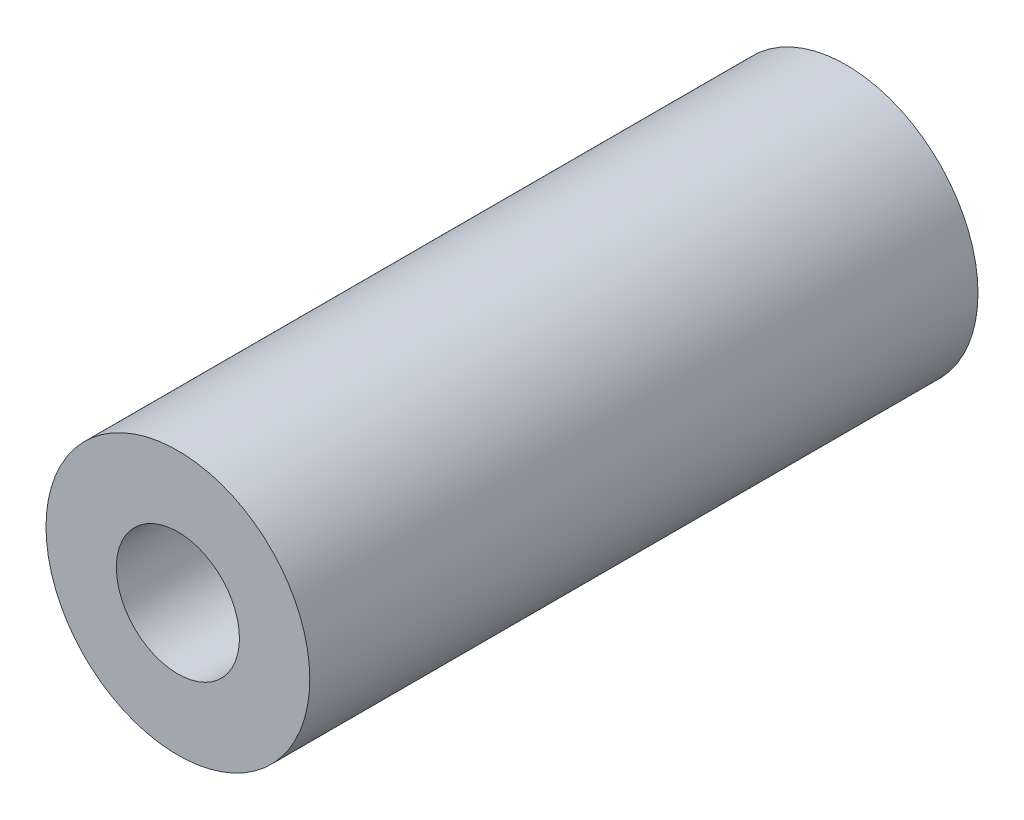
SolidWorks part; units mm, degrees
ref_plane "Front Plane" through (0, 0, 0) normal (0, 0, 1) x (1, 0, 0)
ref_plane "Top Plane" through (0, 0, 0) normal (0, 1, 0) x (1, 0, 0)
ref_plane "Right Plane" through (0, 0, 0) normal (1, 0, 0) x (0, 0, -1)
sketch "Sketch1" plane through (0, 0, 0) normal (0, 0, 1) x (1, 0, 0)
  circle A0 centre (0, 0) radius 1.75
  circle A1 centre (0, 0) radius 3.75
  dimension "D1" = 3.5
  dimension "D2" = 7.5
extrude "Boss-Extrude1" add sketch "Sketch1" along normal blind 19
